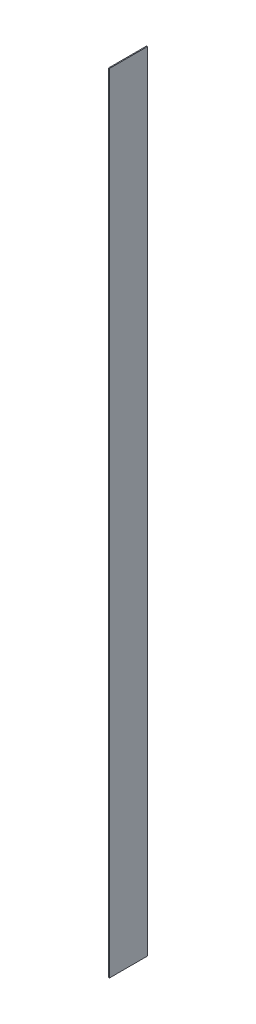
SolidWorks part; units mm, degrees
ref_plane "Front Plane" through (0, 0, 0) normal (0, 0, 1) x (1, 0, 0)
ref_plane "Top Plane" through (0, 0, 0) normal (0, 1, 0) x (1, 0, 0)
ref_plane "Right Plane" through (0, 0, 0) normal (1, 0, 0) x (0, 0, -1)
sketch "Sketch1" plane through (0, 0, 0) normal (1, 0, 0) x (0, 0, -1)
  line L1 (-25.4, 0) -> (25.4, 0)
  line L2 (-25.4, 0) -> (-25.4, 1054.1)
  line L3 (-25.4, 1054.1) -> (25.4, 1054.1)
  line L4 (25.4, 0) -> (25.4, 1054.1)
  dimension "D1" = 50.8
  dimension "D2" = 1054.1
extrude "Boss-Extrude1" add sketch "Sketch1" along normal blind 1.27
